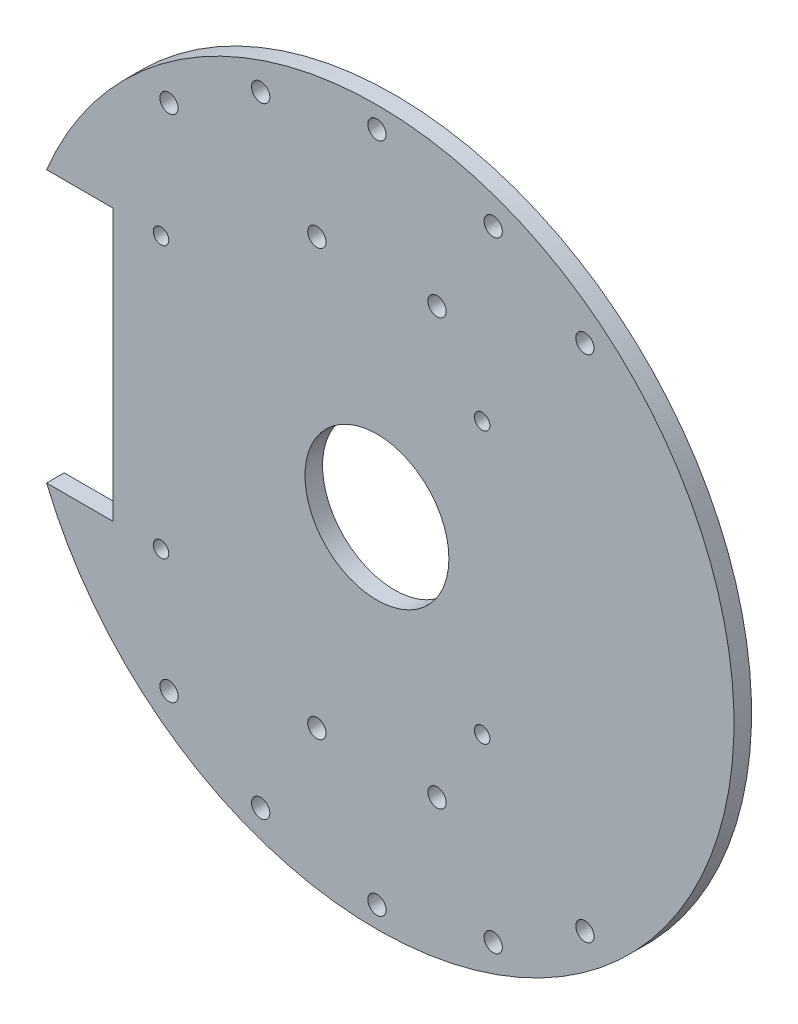
SolidWorks part; units mm, degrees
material "Acrylic (Medium-high impact)"
ref_plane "Front Plane" through (0, 0, 0) normal (0, 0, 1) x (1, 0, 0)
ref_plane "Top Plane" through (0, 0, 0) normal (0, 1, 0) x (1, 0, 0)
ref_plane "Right Plane" through (0, 0, 0) normal (1, 0, 0) x (0, 0, -1)
sketch "Sketch1" plane through (0, 0, 0) normal (0, 0, 1) x (-1, 0, 0)
  line L0 (54.1686, -24.1336) -> (57.6686, -24.1336) construction
  line L1 (57.6686, -24.1336) -> (57.6686, 24.8664) construction
  line L2 (15.1686, 64.8664) -> (15.1686, -64.1336) construction
  line L5 (79.6686, 0.3664) -> (-49.3314, 0.3664) construction
  line L6 (54.1686, -24.1336) -> (54.1686, 24.8664) construction
  line L7 (54.1686, 24.8664) -> (-3.8314, 24.8664) construction
  line L8 (-3.8314, 24.8664) -> (-3.8314, -24.1336) construction
  line L9 (-3.8314, -24.1336) -> (54.1686, -24.1336) construction
  line L12 (57.6686, 24.8664) -> (54.1686, 24.8664) construction
  line L13 (-3.8314, -24.1336) -> (-27.3314, -24.1336) construction
  line L14 (-27.3314, -24.1336) -> (-27.3314, 24.8664) construction
  line L15 (-27.3314, 24.8664) -> (-3.8314, 24.8664) construction
  circle A1 centre (15.1686, 0.3664) radius 64.5
  circle A2 centre (15.1686, -60.2836) radius 1.65
  circle A3 centre (15.1686, 61.0164) radius 1.65
  circle A5 centre (26.0186, -38.0586) radius 1.65
  circle A7 centre (4.3186, -38.0586) radius 1.65
  circle A8 centre (26.0186, 38.7914) radius 1.65
  circle A9 centre (4.3186, 38.7914) radius 1.65
  circle A10 centre (15.1686, 0.3664) radius 13
  circle A11 centre (54.1686, -24.1336) radius 1.4
  circle A12 centre (54.1686, 24.8664) radius 1.4
  circle A13 centre (-3.8314, -24.1336) radius 1.4
  circle A14 centre (-3.8314, 24.8664) radius 1.4
  circle A15 centre (-5.8314, 56.3664) radius 1.65
  circle A16 centre (-22.3949, 46.3664) radius 1.65
  circle A17 centre (36.1686, 56.3664) radius 1.65
  circle A18 centre (52.7321, 46.3664) radius 1.65
  circle A19 centre (52.7321, -45.6336) radius 1.65
  circle A20 centre (36.1686, -55.6336) radius 1.65
  circle A21 centre (-5.8314, -55.6336) radius 1.65
  circle A22 centre (-22.3949, -45.6336) radius 1.65
  point P48 (0, 0)
  dimension "D3" = 23.5
  dimension "D1" = 3.3
  dimension "D4" = 10.85
  dimension "D9" = 26
  dimension "D10" = 3.3
  dimension "D11" = 56
  dimension "D12" = 46
  dimension "D13" = 2.8
  dimension "D20" = 129
  dimension "D2" = 3.5
  dimension "D5" = 60.65
  dimension "D6" = 21.7
  dimension "D7" = 22.225
  dimension "D8" = 22.225
  dimension "D14" = 21
  dimension "D18" = 85
  dimension "D19" = 49
  dimension "D22" = 22
  dimension "D23" = 22
extrude "Boss-Extrude2" add sketch "Sketch1" along normal blind 3.175
sketch "Sketch2" plane through (0, 0, 3.175) normal (0, 0, 1) x (1, 0, 0)
  line L0 (-74.8343, 24.1336) -> (-62.8343, 24.1336)
  line L1 (-62.8343, 24.1336) -> (-62.8343, -24.8664)
  line L2 (-62.8343, -24.8664) -> (-74.8343, -24.8664)
  circle A0 centre (-15.1686, -0.3664) radius 64.5 construction
  arc A1 (-74.8343, -24.8664) -> (-74.8343, 24.1336) centre (-15.1686, -0.3664) cw
  dimension "D3" = 64.5
  dimension "D1" = 49
  dimension "D2" = 12
extrude "Cut-Extrude1" cut sketch "Sketch2" against normal blind 3.175
